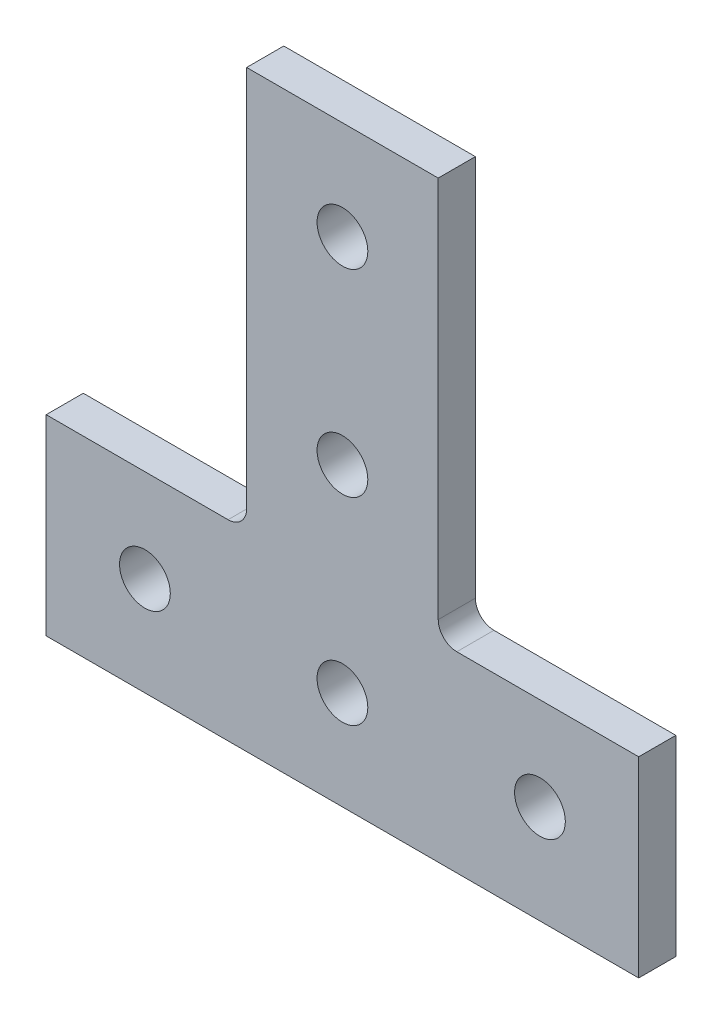
SolidWorks part; units mm, degrees
ref_plane "Front Plane" through (0, 0, 0) normal (0, 0, 1) x (1, 0, 0)
ref_plane "Top Plane" through (0, 0, 0) normal (0, 1, 0) x (1, 0, 0)
ref_plane "Right Plane" through (0, 0, 0) normal (1, 0, 0) x (0, 0, -1)
ref_plane "Plane1" through (0, 0, 0) normal (0, 0, 1) x (1, 0, 0)
sketch "Sketch1" plane through (0, 0, 0) normal (0, 0, 1) x (1, 0, 0)
  line L0 (-38.1, 0) -> (38.1, 0)
  line L1 (38.1, 0) -> (38.1, 24.638)
  line L2 (38.1, 24.638) -> (14.7066, 24.638)
  line L3 (12.319, 27.0256) -> (12.319, 76.2)
  line L4 (12.319, 76.2) -> (-12.319, 76.2)
  line L5 (-12.319, 76.2) -> (-12.319, 27.0256)
  line L6 (-14.7066, 24.638) -> (-38.1, 24.638)
  line L7 (-38.1, 24.638) -> (-38.1, 0)
  arc A0 (14.7066, 24.638) -> (12.319, 27.0256) centre (14.7066, 27.0256) cw
  arc A1 (-12.319, 27.0256) -> (-14.7066, 24.638) centre (-14.7066, 27.0256) cw
  circle A2 centre (25.4, 12.7) radius 3.2639
  circle A3 centre (0, 38.1) radius 3.2639
  circle A4 centre (0, 63.5) radius 3.2639
  circle A5 centre (0, 12.7) radius 3.2639
  circle A6 centre (-25.4, 12.7) radius 3.2639
extrude "Boss-Extrude1" add sketch "Sketch1" along normal blind 4.7752
ref_plane "Plane2" through (0, 12.319, 0) normal (0, -1, 0) x (-1, 0, 0)
